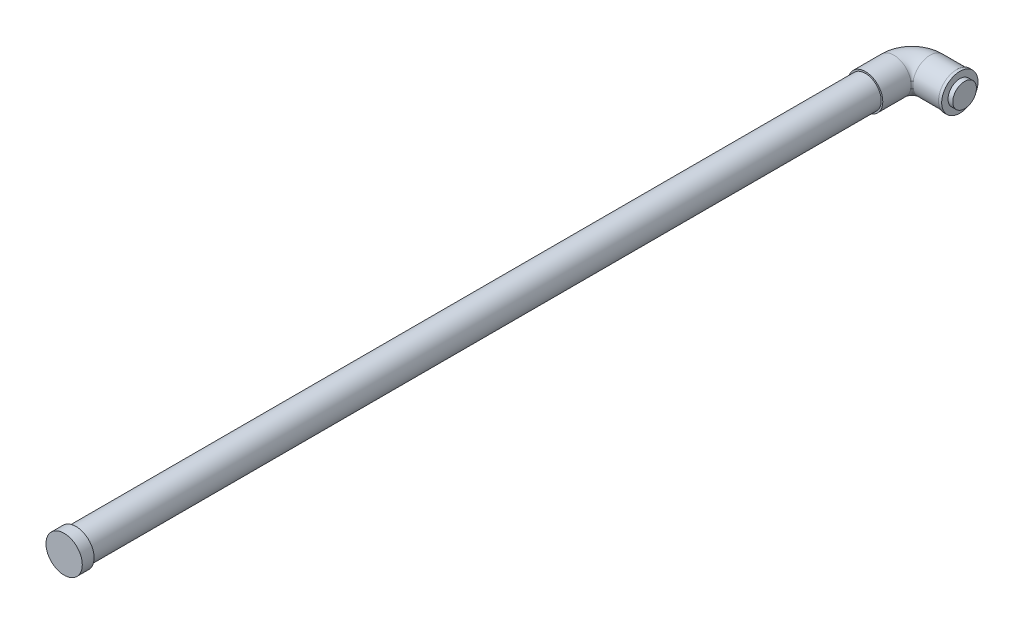
SolidWorks part; units mm, degrees
ref_plane "Front Plane" through (0, 0, 0) normal (0, 0, 1) x (1, 0, 0)
ref_plane "Top Plane" through (0, 0, 0) normal (0, 1, 0) x (1, 0, 0)
ref_plane "Right Plane" through (0, 0, 0) normal (1, 0, 0) x (0, 0, -1)
sketch "Sketch1" plane through (0, 0, 0) normal (0, 1, 0) x (1, 0, 0)
  line L0 (-112.2991, 84.4808) -> (-112.2991, 73.9808)
  line L1 (-100.7991, 95.9808) -> (-83.9991, 95.9808)
  arc A0 (-100.7991, 95.9808) -> (-112.2991, 84.4808) centre (-100.7991, 84.4808) ccw
  dimension "D1" = 11.5
sweep "Sweep1" add path "Sketch1" circular profile diameter 22 parameters "D3"=22
sketch "Sketch34" plane through (0, 0, -73.9808) normal (0, 0, 1) x (1, 0, 0)
  circle A0 centre (-112.2991, 0) radius 11
  dimension "D1" = 22
extrude "Boss-Extrude1" add sketch "Sketch34" along normal blind 7.5
sketch "Sketch41" plane through (-83.9991, 0, 0) normal (1, 0, 0) x (0, 0, -1)
  circle A0 centre (95.9808, 0) radius 11.5
  dimension "D1" = 23
extrude "Boss-Extrude2" add sketch "Sketch41" along normal blind 2
sketch "Sketch42" plane through (0, 0, -66.4808) normal (0, 0, 1) x (1, 0, 0)
  circle A0 centre (-112.2991, 0) radius 10
  dimension "D1" = 20
extrude "Boss-Extrude3" add sketch "Sketch42" along normal blind 500
sketch "Sketch43" plane through (0, 0, 433.5192) normal (0, 0, 1) x (1, 0, 0)
  circle A0 centre (-112.2991, 0) radius 11.5
  dimension "D1" = 23
extrude "Boss-Extrude4" add sketch "Sketch43" along normal blind 7.5
sketch "Sketch129" plane through (-81.9991, 0, 0) normal (1, 0, 0) x (0, 0, -1)
  circle A2 centre (95.9808, 0) radius 7.5
  circle A3 centre (95.9808, 0) radius 7.5
  dimension "D1" = 4
extrude "Boss-Extrude5" add sketch "Sketch129" along normal blind 3
sketch "Sketch130" plane through (0, 0, 441.0192) normal (0, 0, 1) x (1, 0, 0)
  circle A0 centre (-112.2991, 0) radius 9.5 construction
  circle A3 centre (-112.2991, 0) radius 10.5
  circle A4 centre (-112.2991, 0) radius 10.5
  dimension "D2" = 1
  dimension "D1" = 1
extrude "Boss-Extrude6" [suppressed] add sketch "Sketch130" along normal blind 100
